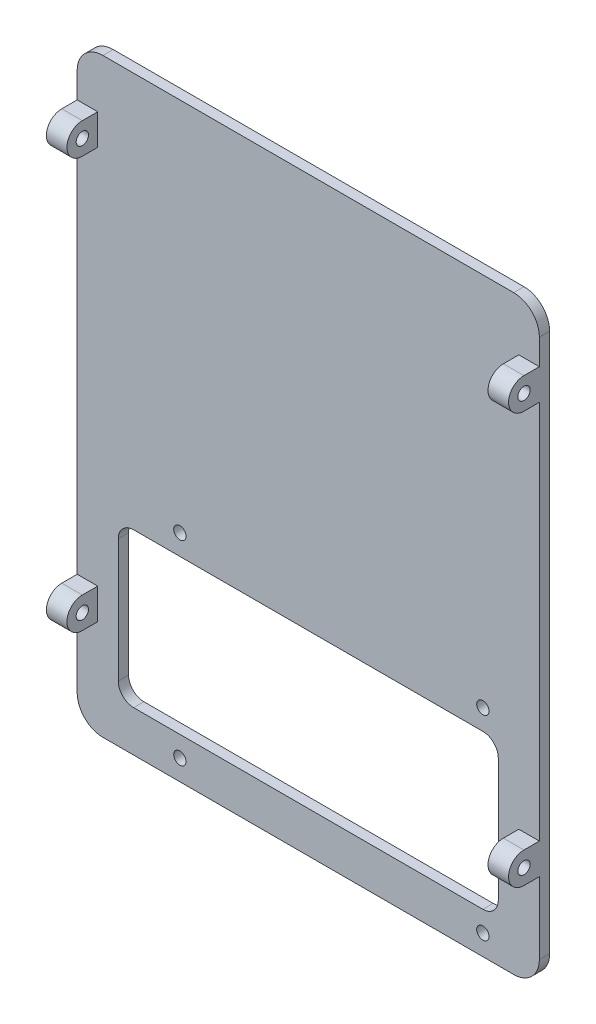
SolidWorks part; units mm, degrees
ref_plane "Front Plane" through (0, 0, 0) normal (0, 0, 1) x (1, 0, 0)
ref_plane "Top Plane" through (0, 0, 0) normal (0, 1, 0) x (1, 0, 0)
ref_plane "Right Plane" through (0, 0, 0) normal (1, 0, 0) x (0, 0, -1)
sketch "Sketch1" plane through (0, 0, 0) normal (1, 0, 0) x (0, 0, -1)
  line L0 (0, 46.99) -> (3.81, 46.99)
  line L1 (3.81, 46.99) -> (3.81, 54.61)
  line L2 (3.81, 54.61) -> (0, 54.61)
  line L3 (55, 0) -> (-55, 0) construction
  line L4 (3.81, -54.61) -> (0, -54.61)
  line L5 (3.81, -46.99) -> (3.81, -54.61)
  line L6 (0, -46.99) -> (3.81, -46.99)
  circle A0 centre (0, 50.8) radius 1.524
  arc A2 (0, 54.61) -> (0, 46.99) centre (0, 50.8) ccw
  arc A3 (0, -54.61) -> (0, -46.99) centre (0, -50.8) cw
  circle A4 centre (0, -50.8) radius 1.524
  point P10 (3.81, 50.8)
  dimension "D1" = 3.048
  dimension "D3" = 3.81
  dimension "D2" = 50.8
  dimension "D4" = 3.81
extrude "Screw holes" add sketch "Sketch1" along normal blind 5.08
sketch "Sketch2" plane through (0, 0, 0) normal (-1, 0, 0) x (0, 0, 1)
  line L0 (-3.81, 46.99) -> (-3.81, 54.61) construction
  line L1 (-3.81, 67.31) -> (-6.35, 67.31)
  line L2 (-3.81, 67.31) -> (-3.81, -78.74)
  line L3 (-3.81, -78.74) -> (-6.35, -78.74)
  line L4 (-6.35, 67.31) -> (-6.35, -78.74)
  dimension "D1" = 2.54
  dimension "D2" = 146.05
  dimension "D3" = 12.7
extrude "Main extrude" add sketch "Sketch2" against normal blind 114.3
ref_plane "Plane1" through (57.15, 0, 0) normal (-1, 0, 0) x (0, 0, 1)
mirror "Screw holes 2" about plane through (57.15, 0, 0) normal (-1, 0, 0) of "Screw holes"
fillet "Fillet1" radius 6.35 4 edges at (0, -78.74, -5.08) (114.3, -78.74, -5.08) (114.3, 67.31, -5.08) (0, 67.31, -5.08)
sketch "Sketch3" plane through (0, 0, -3.81) normal (0, 0, 1) x (1, 0, 0)
  line L1 (25.4, -25.4) -> (100.33, -25.4) construction
  line L2 (25.4, -25.4) -> (25.4, -73.66) construction
  line L3 (25.4, -73.66) -> (100.33, -73.66) construction
  line L4 (100.33, -25.4) -> (100.33, -73.66) construction
  line L6 (0, -46.99) -> (0, 46.99) construction
  line L10 (107.95, -78.74) -> (6.35, -78.74) construction
  circle A0 centre (25.4, -25.4) radius 1.524
  circle A1 centre (100.33, -25.4) radius 1.524
  circle A2 centre (100.33, -73.66) radius 1.524
  circle A3 centre (25.4, -73.66) radius 1.524
  dimension "D5" = 3.048
  dimension "D1" = 48.26
  dimension "D2" = 74.93
  dimension "D3" = 25.4
  dimension "D4" = 5.08
extrude "Component mount holes" cut sketch "Sketch3" against normal through all both and the other way through all
sketch "Sketch4" plane through (0, 0, -3.81) normal (0, 0, 1) x (1, 0, 0)
  line L0 (5.08, -54.61) -> (5.08, -46.99) construction
  line L1 (10.16, -30.48) -> (104.14, -30.48)
  line L2 (10.16, -30.48) -> (10.16, -68.58)
  line L3 (10.16, -68.58) -> (104.14, -68.58)
  line L4 (104.14, -30.48) -> (104.14, -68.58)
  line L5 (109.22, -46.99) -> (109.22, -54.61) construction
  circle A0 centre (25.4, -25.4) radius 1.524 construction
  circle A1 centre (25.4, -73.66) radius 1.524 construction
  point P10 (5.08, -50.8)
  dimension "D1" = 5.08
  dimension "D2" = 5.08
  dimension "D3" = 5.08
  dimension "D4" = 5.08
extrude "Weight reduction" cut sketch "Sketch4" against normal through all both and the other way through all
fillet "Fillet2" radius 3.81 4 edges at (10.16, -68.58, -5.08) (104.14, -68.58, -5.08) (104.14, -30.48, -5.08) (10.16, -30.48, -5.08)
